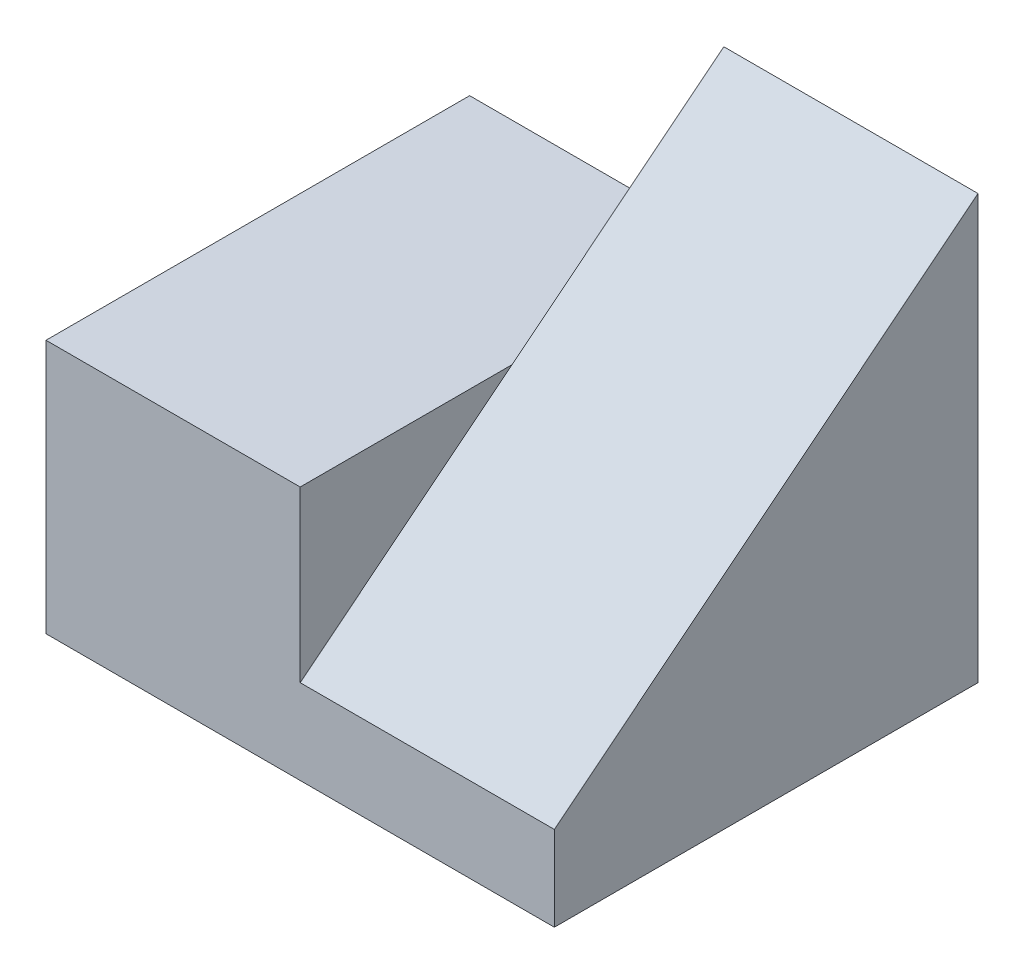
SolidWorks part; units mm, degrees
ref_plane "Front Plane" through (0, 0, 0) normal (0, 0, 1) x (1, 0, 0)
ref_plane "Top Plane" through (0, 0, 0) normal (0, 1, 0) x (1, 0, 0)
ref_plane "Right Plane" through (0, 0, 0) normal (1, 0, 0) x (0, 0, -1)
sketch "Sketch1" plane through (0, 0, 0) normal (0, 0, 1) x (1, 0, 0)
  line L0 (0, 0) -> (0, 15)
  line L1 (0, 15) -> (15, 15)
  line L2 (15, 15) -> (15, 5)
  line L3 (15, 5) -> (30, 5)
  line L4 (30, 5) -> (30, 0)
  line L5 (30, 0) -> (0, 0)
  dimension "D1" = 15
  dimension "D2" = 15
  dimension "D3" = 5
  dimension "D4" = 15
extrude "Boss-Extrude1" add sketch "Sketch1" along normal blind 25
sketch "Sketch2" plane through (15, 0, 0) normal (1, 0, 0) x (0, 0, -1)
  line L0 (-25, 5) -> (0, 25)
  line L1 (0, 25) -> (0, 5)
  line L2 (0, 5) -> (-25, 5)
  dimension "D1" = 20
extrude "Boss-Extrude2" add sketch "Sketch2" along normal blind 15
